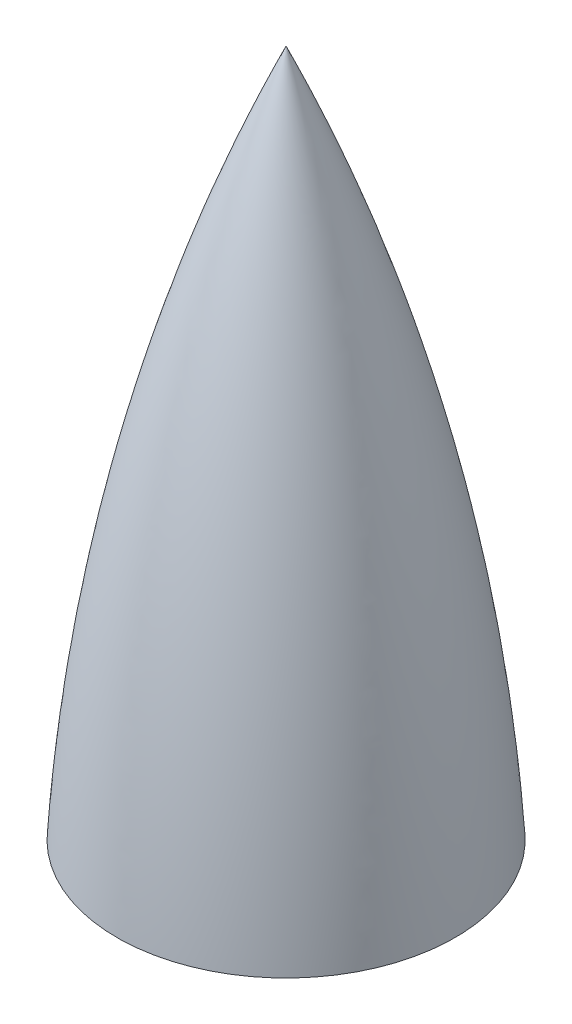
SolidWorks part; units mm, degrees
material "PVB"
ref_plane "Front Plane" through (0, 0, 0) normal (0, 0, 1) x (1, 0, 0)
ref_plane "Top Plane" through (0, 0, 0) normal (0, 1, 0) x (1, 0, 0)
ref_plane "Right Plane" through (0, 0, 0) normal (1, 0, 0) x (0, 0, -1)
sketch "Sketch2" plane through (0, 0, 0) normal (0, 0, 1) x (1, 0, 0)
  line L0 (0, 0) -> (0, 381) construction
  line L1 (-93.6625, 0) -> (-88.9, 0)
  line L2 (0, 381) -> (0, 375.92)
  arc A0 (0, 381) -> (-93.6625, 0) centre (997.6877, -66.2776) ccw
  arc A1 (0, 375.92) -> (-88.9, 0) centre (1114.6958, -86.1623) ccw
  dimension "D1" = 381
  dimension "D2" = 5.08
  dimension "D3" = 93.6625
revolve "Revolve1" add sketch "Sketch2" angle 360 about L2
sketch "Sketch3" plane through (0, 0, 0) normal (0, -1, 0) x (1, 0, 0)
  circle A0 centre (0, 0) radius 88.9
  circle A1 centre (0, 0) radius 86.995
  dimension "D1" = 177.8
extrude "Boss-Extrude1" [suppressed] add sketch "Sketch3" along normal blind 35.56
